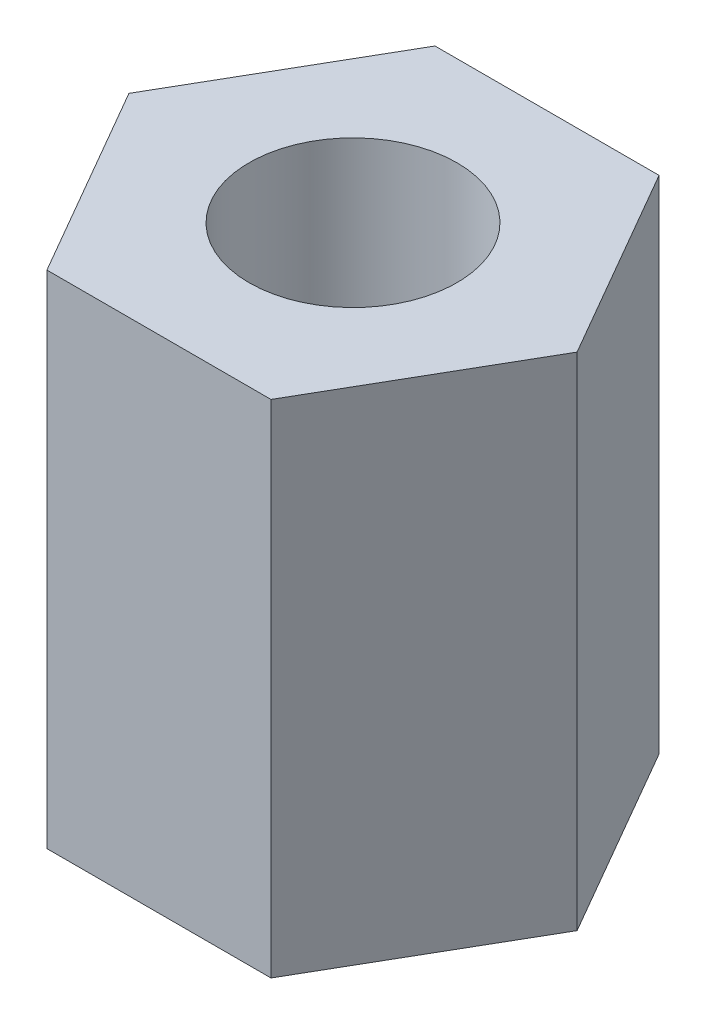
SolidWorks part; units mm, degrees
ref_plane "前视基准面" through (0, 0, 0) normal (0, 0, 1) x (1, 0, 0)
ref_plane "上视基准面" through (0, 0, 0) normal (0, 1, 0) x (1, 0, 0)
ref_plane "右视基准面" through (0, 0, 0) normal (1, 0, 0) x (0, 0, -1)
sketch "草图1" plane through (0, 0, 0) normal (0, 1, 0) x (1, 0, 0)
  line L7 (3.2332, 0) -> (1.6166, 2.8)
  line L8 (1.6166, 2.8) -> (-1.6166, 2.8)
  line L9 (-1.6166, 2.8) -> (-3.2332, 0)
  line L10 (-3.2332, 0) -> (-1.6166, -2.8)
  line L11 (-1.6166, -2.8) -> (1.6166, -2.8)
  line L12 (1.6166, -2.8) -> (3.2332, 0)
  circle A0 centre (0, 0) radius 2.8 construction
  circle A1 centre (0, 0) radius 1.5
  dimension "D2" = 3
  dimension "D1" = 5.6
extrude "凸台-拉伸1" add sketch "草图1" along normal blind 7.23
